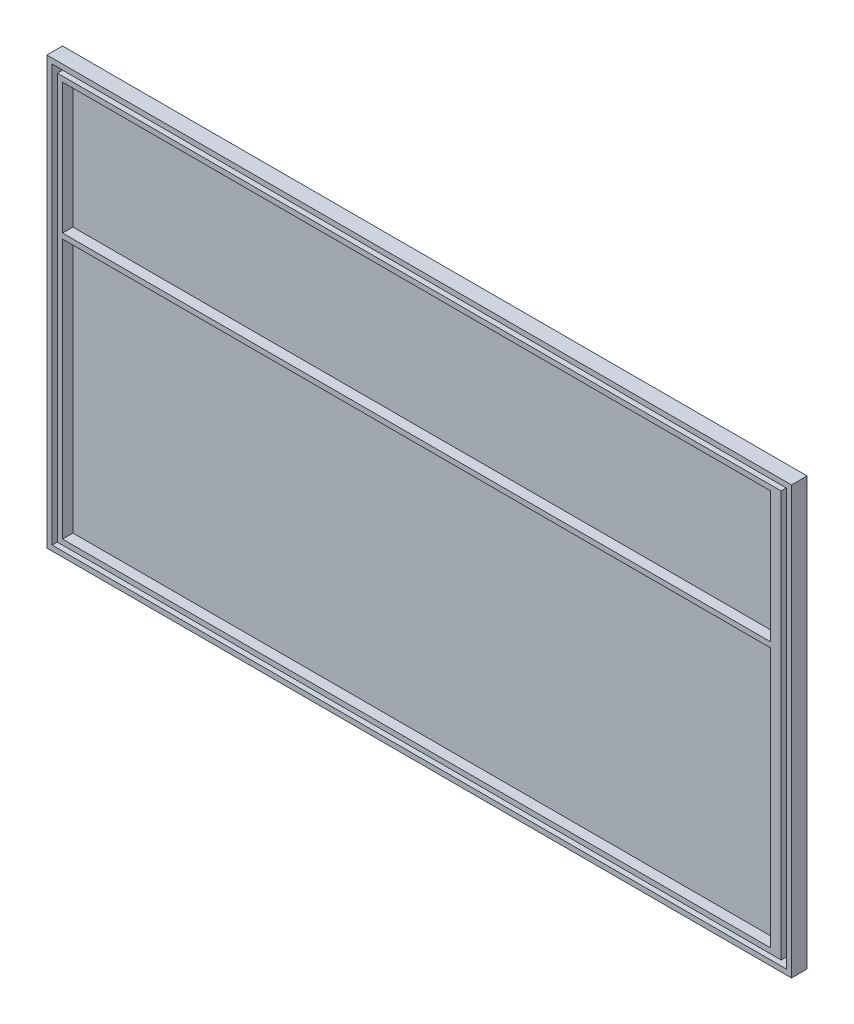
SolidWorks part; units mm, degrees
ref_plane "Alzado" through (0, 0, 0) normal (0, 0, 1) x (1, 0, 0)
ref_plane "Planta" through (0, 0, 0) normal (0, 1, 0) x (1, 0, 0)
ref_plane "Vista lateral" through (0, 0, 0) normal (1, 0, 0) x (0, 0, -1)
sketch "Croquis1" plane through (0, 0, 0) normal (0, 0, 1) x (1, 0, 0)
  line L1 (-171.0228, 55.2939) -> (-28.0228, 55.2939)
  line L2 (-171.0228, 55.2939) -> (-171.0228, -26.7061)
  line L3 (-171.0228, -26.7061) -> (-28.0228, -26.7061)
  line L4 (-28.0228, 55.2939) -> (-28.0228, -26.7061)
  dimension "D1" = 143
  dimension "D2" = 82
extrude "Saliente-Extruir1" add sketch "Croquis1" along normal blind 1
sketch "Croquis2" plane through (0, 0, 1) normal (0, 0, 1) x (1, 0, 0)
  line L0 (-171.0228, -26.7061) -> (-171.0228, 55.2939)
  line L1 (-171.0228, 55.2939) -> (-28.0228, 55.2939)
  line L2 (-28.0228, 55.2939) -> (-28.0228, -26.7061)
  line L3 (-28.0228, -26.7061) -> (-171.0228, -26.7061)
  line L4 (-99.5228, 54.2939) -> (-99.5228, 39.2939) construction
  line L5 (-170.0228, 54.2939) -> (-29.0228, 54.2939)
  line L6 (-170.0228, 54.2939) -> (-170.0228, -25.7061)
  line L7 (-170.0228, -25.7061) -> (-29.0228, -25.7061)
  line L8 (-29.0228, 54.2939) -> (-29.0228, -25.7061)
  line L9 (-169.0228, 53.2939) -> (-30.0228, 53.2939)
  line L10 (-169.0228, 53.2939) -> (-169.0228, -24.7061)
  line L11 (-169.0228, -24.7061) -> (-30.0228, -24.7061)
  line L12 (-30.0228, 53.2939) -> (-30.0228, -24.7061)
  line L18 (-168.0228, 27.1898) -> (-32.0228, 27.1898)
  line L23 (-168.0228, 52.2939) -> (-32.0228, 52.2939)
  line L25 (-168.0228, -23.7061) -> (-32.0228, -23.7061)
  line L27 (-32.0228, 26.1898) -> (-168.0228, 26.1898)
  line L28 (-168.0228, 26.1898) -> (-168.0228, -23.7061)
  line L29 (-168.0228, 27.1898) -> (-168.0228, 52.2939)
  line L30 (-32.0228, 52.2939) -> (-32.0228, 27.1898)
  line L31 (-32.0228, 26.1898) -> (-32.0228, -23.7061)
  dimension "D1" = 1
  dimension "D2" = 1
  dimension "D3" = 1
  dimension "D4" = 1
  dimension "D5" = 1
  dimension "D6" = 1
  dimension "D7" = 1
  dimension "D8" = 1
  dimension "D16" = 1
  dimension "D18" = 1
extrude "Saliente-Extruir2" add sketch "Croquis2" along normal blind 2
